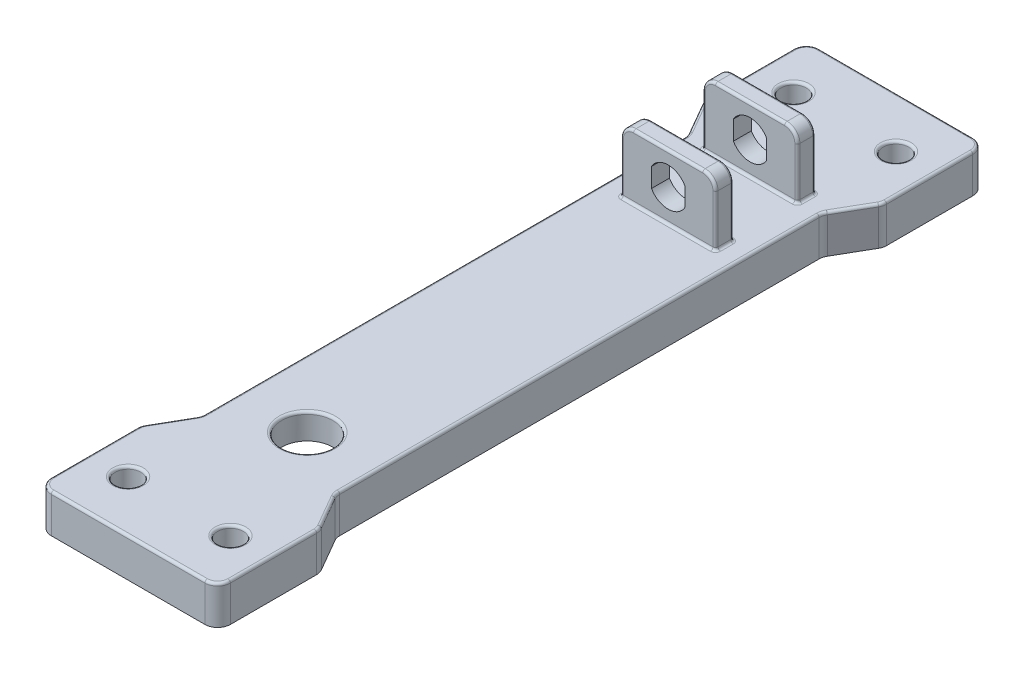
SolidWorks part; units mm, degrees
ref_plane "Front Plane" through (0, 0, 0) normal (0, 0, 1) x (1, 0, 0)
ref_plane "Top Plane" through (0, 0, 0) normal (0, 1, 0) x (1, 0, 0)
ref_plane "Right Plane" through (0, 0, 0) normal (1, 0, 0) x (0, 0, -1)
sketch "Sketch1" plane through (0, 0, 0) normal (0, 1, 0) x (1, 0, 0)
  line L0 (0, 150) -> (0, -150) construction
  line L1 (-35, 150) -> (35, 150)
  line L2 (-35, 150) -> (-35, 110)
  line L3 (-35, -150) -> (35, -150)
  line L4 (35, 150) -> (35, 110)
  line L5 (-35, 150) -> (35, -150) construction
  line L6 (-35, -150) -> (35, 150) construction
  line L7 (-35, 110) -> (-26.3397, 95)
  line L8 (-26.3397, 95) -> (-26.3397, -95)
  line L9 (-26.3397, -95) -> (-35, -110)
  line L10 (26.3397, -95) -> (35, -110)
  line L11 (26.3397, 95) -> (26.3397, -95)
  line L12 (35, 110) -> (26.3397, 95)
  line L13 (-35, -110) -> (-35, -150)
  line L14 (35, -110) -> (35, -150)
  point P0 (0, 0)
  dimension "D1" = 300
  dimension "D2" = 70
  dimension "D3" = 30
  dimension "D4" = 40
  dimension "D5" = 40
  dimension "D6" = 190
extrude "Boss-Extrude1" add sketch "Sketch1" along normal blind 15
fillet "Fillet1" radius 5 12 edges at (-35, 7.5, 150) (-35, 7.5, 110) (-26.3397, 7.5, 95) (-26.3397, 7.5, -95) (-35, 7.5, -110) (-35, 7.5, -150) (35, 7.5, -150) (35, 7.5, -110) (26.3397, 7.5, -95) (26.3397, 7.5, 95) (35, 7.5, 110) (35, 7.5, 150)
sketch "Sketch2" plane through (0, 0, 0) normal (0, -1, 0) x (1, 0, 0)
  line L24 (25, 140) -> (-25, 140)
  line L25 (-25, 140) -> (-25, 112.6795)
  line L26 (-25, 112.6795) -> (-18.3494, 101.1603)
  line L27 (-16.3397, 93.6603) -> (-16.3397, -93.6603)
  line L28 (-18.3494, -101.1603) -> (-25, -112.6795)
  line L29 (-25, -112.6795) -> (-25, -140)
  line L30 (-25, -140) -> (25, -140)
  line L31 (25, -140) -> (25, -112.6795)
  line L32 (25, -112.6795) -> (18.3494, -101.1603)
  line L33 (16.3397, -93.6603) -> (16.3397, 93.6603)
  line L34 (18.3494, 101.1603) -> (25, 112.6795)
  line L35 (25, 112.6795) -> (25, 140)
  line L36 (25, 140) -> (-25, 140)
  line L37 (-25, 140) -> (-25, 112.6795)
  line L38 (-25, 112.6795) -> (-18.3494, 101.1603)
  line L39 (-16.3397, 93.6603) -> (-16.3397, -93.6603)
  line L40 (-18.3494, -101.1603) -> (-25, -112.6795)
  line L41 (-25, -112.6795) -> (-25, -140)
  line L42 (-25, -140) -> (25, -140)
  line L43 (25, -140) -> (25, -112.6795)
  line L44 (25, -112.6795) -> (18.3494, -101.1603)
  line L45 (16.3397, -93.6603) -> (16.3397, 93.6603)
  line L46 (18.3494, 101.1603) -> (25, 112.6795)
  line L47 (25, 112.6795) -> (25, 140)
  arc A24 (-16.3397, 93.6603) -> (-18.3494, 101.1603) centre (-31.3397, 93.6603) ccw
  arc A25 (-18.3494, -101.1603) -> (-16.3397, -93.6603) centre (-31.3397, -93.6603) ccw
  arc A26 (16.3397, -93.6603) -> (18.3494, -101.1603) centre (31.3397, -93.6603) ccw
  arc A27 (18.3494, 101.1603) -> (16.3397, 93.6603) centre (31.3397, 93.6603) ccw
  arc A28 (-16.3397, 93.6603) -> (-18.3494, 101.1603) centre (-31.3397, 93.6603) ccw
  arc A29 (-18.3494, -101.1603) -> (-16.3397, -93.6603) centre (-31.3397, -93.6603) ccw
  arc A30 (16.3397, -93.6603) -> (18.3494, -101.1603) centre (31.3397, -93.6603) ccw
  arc A31 (18.3494, 101.1603) -> (16.3397, 93.6603) centre (31.3397, 93.6603) ccw
  dimension "D1" = 10
extrude "Cut-Extrude1" cut sketch "Sketch2" against normal blind 5
sketch "Sketch3" plane through (0, 15, 0) normal (0, 1, 0) x (1, 0, 0)
  line L0 (0, 150) -> (0, 0) construction
  line L1 (30, 150) -> (-30, 150) construction
  line L3 (-18.5, 100) -> (18.5, 100)
  line L4 (-18.5, 100) -> (-18.5, 93)
  line L5 (-18.5, 93) -> (18.5, 93)
  line L6 (18.5, 100) -> (18.5, 93)
  line L7 (-18.5, 100) -> (18.5, 93) construction
  line L8 (-18.5, 93) -> (18.5, 100) construction
  line L9 (-18.5, 68) -> (18.5, 68)
  line L10 (-18.5, 68) -> (-18.5, 61)
  line L11 (-18.5, 61) -> (18.5, 61)
  line L12 (18.5, 68) -> (18.5, 61)
  line L13 (-18.5, 68) -> (18.5, 61) construction
  line L14 (-18.5, 61) -> (18.5, 68) construction
  point P5 (0, 96.5)
  point P10 (0, 64.5)
  dimension "D1" = 7
  dimension "D2" = 37
  dimension "D3" = 25
  dimension "D4" = 50
extrude "Boss-Extrude2" add sketch "Sketch3" along normal blind 25
fillet "Fillet2" radius 5 4 edges at (18.5, 40, -64.5) (-18.5, 40, -64.5) (18.5, 40, -96.5) (-18.5, 40, -96.5)
fillet "Fillet3" radius 1 28 edges at (18.5, 15, -64.5) (0, 15, -68) (-18.5, 15, -64.5) (0, 15, -61) (0, 40, -68) (0, 40, -61) (-18.5, 25, -61) (-18.5, 25, -68) (18.5, 25, -68) (18.5, 15, -96.5) (0, 15, -100) (-18.5, 15, -96.5) (0, 15, -93) (0, 40, -100) (0, 40, -93) (18.5, 25, -93) (-18.5, 25, -93) (-18.5, 25, -100) (18.5, 25, -100) (-17.0355, 38.5355, -68) (17.0355, 38.5355, -68) (-17.0355, 38.5355, -61) (17.0355, 38.5355, -61) (-17.0355, 38.5355, -100) (17.0355, 38.5355, -100) (-17.0355, 38.5355, -93) (17.0355, 38.5355, -93) (18.5, 25, -61)
sketch "Sketch5" plane through (0, 0, -61) normal (0, 0, 1) x (1, 0, 0)
  line L0 (0, 39) -> (0, 16) construction
  line L1 (13.5, 39) -> (-13.5, 39) construction
  line L2 (-17.5, 16) -> (17.5, 16) construction
  line L3 (19.5, 15) -> (17.5, 15) construction
  line L4 (-6.5, 31.2417) -> (-6.5, 23.7583)
  line L5 (6.5, 31.2417) -> (6.5, 23.7583)
  arc A0 (-6.5, 23.7583) -> (6.5, 23.7583) centre (0, 27.5) ccw
  arc A1 (6.5, 31.2417) -> (-6.5, 31.2417) centre (0, 27.5) ccw
  point P10 (18.5, 15)
  dimension "D2" = 15
  dimension "D1" = 12.5
  dimension "D3" = 6.5
extrude "Cut-Extrude2" cut sketch "Sketch5" against normal through all both and the other way through all
sketch "Sketch6" plane through (0, 15, 0) normal (0, 1, 0) x (1, 0, 0)
  line L0 (0, 150) -> (0, -150) construction
  line L1 (30, 150) -> (-30, 150) construction
  line L2 (-30, -150) -> (30, -150) construction
  line L3 (0, 0) -> (35.278, 0) construction
  circle A0 centre (-20, 130) radius 5
  circle A1 centre (20, 130) radius 5
  circle A2 centre (20, -130) radius 5
  circle A3 centre (-20, -130) radius 5
  circle A4 centre (0, -80) radius 10
  dimension "D3" = 10
  dimension "D5" = 20
  dimension "D1" = 20
  dimension "D2" = 20
  dimension "D4" = 20
  dimension "D6" = 70
extrude "Cut-Extrude3" cut sketch "Sketch6" against normal through all both
fillet "Fillet4" radius 1 29 edges at (-34.8296, 15, 110.0457) (-30.6699, 15, 102.5) (-26.5101, 15, 94.9543) (-26.3397, 15, 0) (-26.5101, 15, -94.9543) (-30.6699, 15, -102.5) (-34.8296, 15, -110.0457) (-35, 15, -128.1699) (-33.5355, 15, -148.5355) (0, 15, -150) (33.5355, 15, -148.5355) (35, 15, -128.1699) (34.8296, 15, -110.0457) (30.6699, 15, -102.5) (26.5101, 15, -94.9543) (26.3397, 15, 0) (26.5101, 15, 94.9543) (30.6699, 15, 102.5) (34.8296, 15, 110.0457) (35, 15, 128.1699) (33.5355, 15, 148.5355) (0, 15, 150) (-33.5355, 15, 148.5355) (-35, 15, 128.1699) (-20, 15, -125) (20, 15, -125) (20, 15, 125) (-20, 15, 125) (0, 15, 90)
